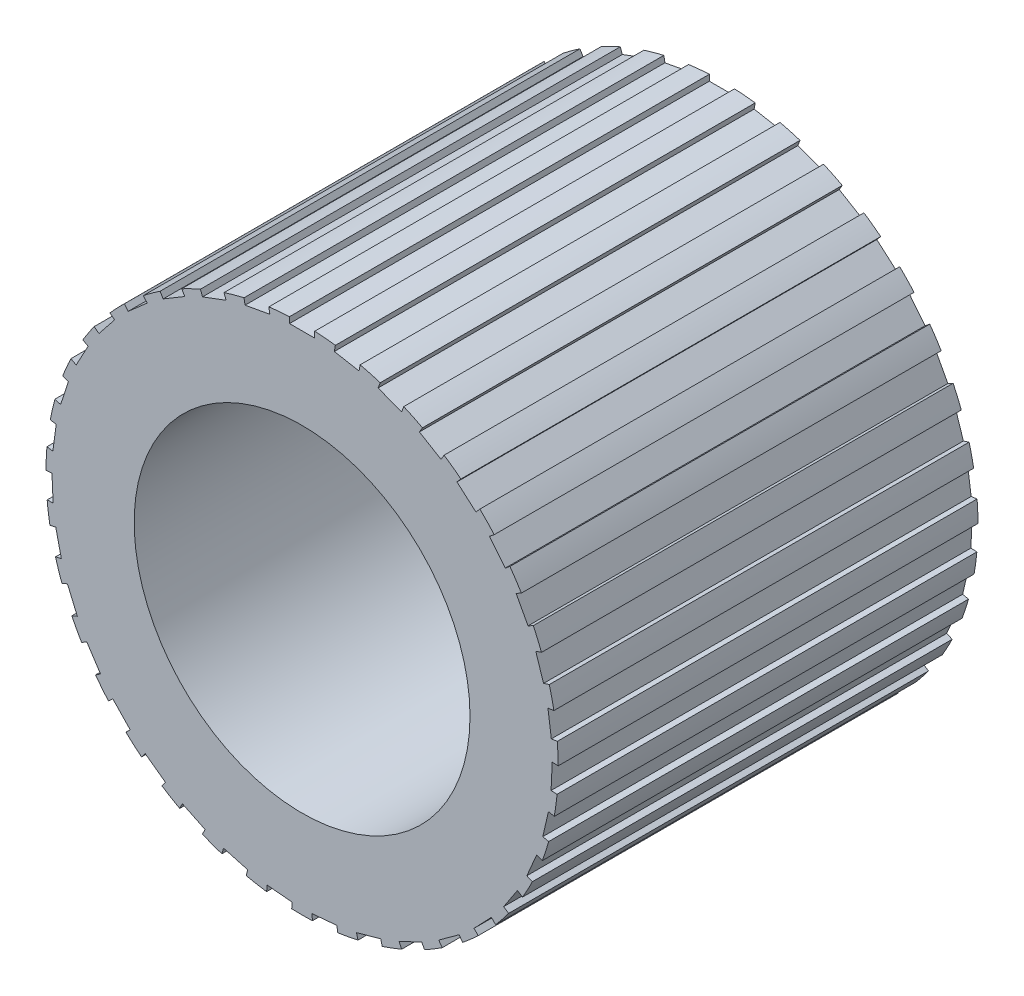
SolidWorks part; units mm, degrees
ref_plane "Plan de face" through (0, 0, 0) normal (0, 0, 1) x (1, 0, 0)
ref_plane "Plan de dessus" through (0, 0, 0) normal (0, 1, 0) x (1, 0, 0)
ref_plane "Plan de droite" through (0, 0, 0) normal (1, 0, 0) x (0, 0, -1)
sketch "Esquisse1" plane through (0, 0, 0) normal (0, 0, 1) x (1, 0, 0)
  circle A0 centre (0, 0) radius 6.1
  circle A1 centre (0, 0) radius 4
  dimension "D1" = 8
  dimension "D2" = 12.2
extrude "Boss.-Extru.1" add sketch "Esquisse1" along normal blind 10 contours A0 | A1
sketch "Esquisse4" plane through (0, 0, 10) normal (0, 0, 1) x (1, 0, 0)
  line L0 (0.7672, 5.9079) -> (0.8208, 6.2031)
  line L1 (-0.3, 5.95) -> (0.3, 5.95)
  line L2 (-0.3, 5.95) -> (-0.3, 6.25)
  line L3 (-0.3, 6.25) -> (0.3, 6.25)
  line L4 (0.3, 5.95) -> (0.3, 6.25)
  line L5 (-0.3, 5.95) -> (0.3, 6.25) construction
  line L6 (-0.3, 6.25) -> (0.3, 5.95) construction
  line L7 (0.7672, 5.9079) -> (1.3576, 5.8008)
  line L8 (1.3576, 5.8008) -> (1.4112, 6.096)
  line L9 (0.8208, 6.2031) -> (1.4112, 6.096)
  line L10 (1.8098, 5.676) -> (1.9152, 5.9569)
  line L11 (1.8098, 5.676) -> (2.3716, 5.4652)
  line L12 (2.3716, 5.4652) -> (2.477, 5.7461)
  line L13 (1.9152, 5.9569) -> (2.477, 5.7461)
  line L14 (2.7942, 5.2616) -> (2.9481, 5.5192)
  line L15 (2.7942, 5.2616) -> (3.3093, 4.9539)
  line L16 (3.3093, 4.9539) -> (3.4632, 5.2114)
  line L17 (2.9481, 5.5192) -> (3.4632, 5.2114)
  line L18 (3.6888, 4.6782) -> (3.8862, 4.9041)
  line L19 (3.6888, 4.6782) -> (4.1407, 4.2834)
  line L20 (4.1407, 4.2834) -> (4.338, 4.5093)
  line L21 (3.8862, 4.9041) -> (4.338, 4.5093)
  line L22 (4.4649, 3.9443) -> (4.6994, 4.1314)
  line L23 (4.4649, 3.9443) -> (4.8389, 3.4752)
  line L24 (4.8389, 3.4752) -> (5.0735, 3.6623)
  line L25 (4.6994, 4.1314) -> (5.0735, 3.6623)
  line L26 (5.0974, 3.0837) -> (5.3616, 3.2259)
  line L27 (5.0974, 3.0837) -> (5.3817, 2.5553)
  line L28 (5.3817, 2.5553) -> (5.6459, 2.6975)
  line L29 (5.3616, 3.2259) -> (5.6459, 2.6975)
  line L30 (5.5661, 2.124) -> (5.8514, 2.2167)
  line L31 (5.5661, 2.124) -> (5.7515, 1.5533)
  line L32 (5.7515, 1.5533) -> (6.0368, 1.646)
  line L33 (5.8514, 2.2167) -> (6.0368, 1.646)
  line L34 (5.8559, 1.096) -> (6.1532, 1.1362)
  line L35 (5.8559, 1.096) -> (5.9364, 0.5014)
  line L36 (5.9364, 0.5014) -> (6.2337, 0.5417)
  line L37 (6.1532, 1.1362) -> (6.2337, 0.5417)
  line L38 (5.9575, 0.0328) -> (6.2572, 0.0193)
  line L39 (5.9575, 0.0328) -> (5.9305, -0.5666)
  line L40 (5.9305, -0.5666) -> (6.2302, -0.5801)
  line L41 (6.2572, 0.0193) -> (6.2302, -0.5801)
  line L42 (5.8676, -1.0315) -> (6.1601, -1.0983)
  line L43 (5.8676, -1.0315) -> (5.7341, -1.6165)
  line L44 (5.7341, -1.6165) -> (6.0265, -1.6832)
  line L45 (6.1601, -1.0983) -> (6.0265, -1.6832)
  line L46 (5.5891, -2.0626) -> (5.865, -2.1805)
  line L47 (5.5891, -2.0626) -> (5.3533, -2.6144)
  line L48 (5.3533, -2.6144) -> (5.6291, -2.7323)
  line L49 (5.865, -2.1805) -> (5.6291, -2.7323)
  line L50 (5.131, -3.0275) -> (5.3814, -3.1927)
  line L51 (5.131, -3.0275) -> (4.8004, -3.5282)
  line L52 (4.8004, -3.5282) -> (5.0508, -3.6935)
  line L53 (5.3814, -3.1927) -> (5.0508, -3.6935)
  line L54 (4.5079, -3.895) -> (4.7248, -4.1023)
  line L55 (4.5079, -3.895) -> (4.0933, -4.3287)
  line L56 (4.0933, -4.3287) -> (4.3101, -4.536)
  line L57 (4.7248, -4.1023) -> (4.3101, -4.536)
  line L58 (3.74, -4.6373) -> (3.9164, -4.88)
  line L59 (3.74, -4.6373) -> (3.2546, -4.99)
  line L60 (3.2546, -4.99) -> (3.431, -5.2327)
  line L61 (3.9164, -4.88) -> (3.431, -5.2327)
  line L62 (2.8519, -5.2306) -> (2.9821, -5.5009)
  line L63 (2.8519, -5.2306) -> (2.3113, -5.4909)
  line L64 (2.3113, -5.4909) -> (2.4415, -5.7612)
  line L65 (2.9821, -5.5009) -> (2.4415, -5.7612)
  line L66 (1.8721, -5.6558) -> (1.9519, -5.945)
  line L67 (1.8721, -5.6558) -> (1.2937, -5.8154)
  line L68 (1.2937, -5.8154) -> (1.3735, -6.1046)
  line L69 (1.9519, -5.945) -> (1.3735, -6.1046)
  line L70 (0.8321, -5.8992) -> (0.859, -6.1979)
  line L71 (0.8321, -5.8992) -> (0.2346, -5.9529)
  line L72 (0.2346, -5.9529) -> (0.2615, -6.2517)
  line L73 (0.859, -6.1979) -> (0.2615, -6.2517)
  line L74 (-0.2346, -5.9529) -> (-0.2615, -6.2517)
  line L75 (-0.2346, -5.9529) -> (-0.8321, -5.8992)
  line L76 (-0.8321, -5.8992) -> (-0.859, -6.1979)
  line L77 (-0.2615, -6.2517) -> (-0.859, -6.1979)
  line L78 (-1.2937, -5.8154) -> (-1.3735, -6.1046)
  line L79 (-1.2937, -5.8154) -> (-1.8721, -5.6558)
  line L80 (-1.8721, -5.6558) -> (-1.9519, -5.945)
  line L81 (-1.3735, -6.1046) -> (-1.9519, -5.945)
  line L82 (-2.3113, -5.4909) -> (-2.4415, -5.7612)
  line L83 (-2.3113, -5.4909) -> (-2.8519, -5.2306)
  line L84 (-2.8519, -5.2306) -> (-2.9821, -5.5009)
  line L85 (-2.4415, -5.7612) -> (-2.9821, -5.5009)
  line L86 (-3.2546, -4.99) -> (-3.431, -5.2327)
  line L87 (-3.2546, -4.99) -> (-3.74, -4.6373)
  line L88 (-3.74, -4.6373) -> (-3.9164, -4.88)
  line L89 (-3.431, -5.2327) -> (-3.9164, -4.88)
  line L90 (-4.0933, -4.3287) -> (-4.3101, -4.536)
  line L91 (-4.0933, -4.3287) -> (-4.5079, -3.895)
  line L92 (-4.5079, -3.895) -> (-4.7248, -4.1023)
  line L93 (-4.3101, -4.536) -> (-4.7248, -4.1023)
  line L94 (-4.8004, -3.5282) -> (-5.0508, -3.6935)
  line L95 (-4.8004, -3.5282) -> (-5.131, -3.0275)
  line L96 (-5.131, -3.0275) -> (-5.3814, -3.1927)
  line L97 (-5.0508, -3.6935) -> (-5.3814, -3.1927)
  line L98 (-5.3533, -2.6144) -> (-5.6291, -2.7323)
  line L99 (-5.3533, -2.6144) -> (-5.5891, -2.0626)
  line L100 (-5.5891, -2.0626) -> (-5.865, -2.1805)
  line L101 (-5.6291, -2.7323) -> (-5.865, -2.1805)
  line L102 (-5.7341, -1.6165) -> (-6.0265, -1.6832)
  line L103 (-5.7341, -1.6165) -> (-5.8676, -1.0315)
  line L104 (-5.8676, -1.0315) -> (-6.1601, -1.0983)
  line L105 (-6.0265, -1.6832) -> (-6.1601, -1.0983)
  line L106 (-5.9305, -0.5666) -> (-6.2302, -0.5801)
  line L107 (-5.9305, -0.5666) -> (-5.9575, 0.0328)
  line L108 (-5.9575, 0.0328) -> (-6.2572, 0.0193)
  line L109 (-6.2302, -0.5801) -> (-6.2572, 0.0193)
  line L110 (-5.9364, 0.5014) -> (-6.2337, 0.5417)
  line L111 (-5.9364, 0.5014) -> (-5.8559, 1.096)
  line L112 (-5.8559, 1.096) -> (-6.1532, 1.1362)
  line L113 (-6.2337, 0.5417) -> (-6.1532, 1.1362)
  line L114 (-5.7515, 1.5533) -> (-6.0368, 1.646)
  line L115 (-5.7515, 1.5533) -> (-5.5661, 2.124)
  line L116 (-5.5661, 2.124) -> (-5.8514, 2.2167)
  line L117 (-6.0368, 1.646) -> (-5.8514, 2.2167)
  line L118 (-5.3817, 2.5553) -> (-5.6459, 2.6975)
  line L119 (-5.3817, 2.5553) -> (-5.0974, 3.0837)
  line L120 (-5.0974, 3.0837) -> (-5.3616, 3.2259)
  line L121 (-5.6459, 2.6975) -> (-5.3616, 3.2259)
  line L122 (-4.8389, 3.4752) -> (-5.0735, 3.6623)
  line L123 (-4.8389, 3.4752) -> (-4.4649, 3.9443)
  line L124 (-4.4649, 3.9443) -> (-4.6994, 4.1314)
  line L125 (-5.0735, 3.6623) -> (-4.6994, 4.1314)
  line L126 (-4.1407, 4.2834) -> (-4.338, 4.5093)
  line L127 (-4.1407, 4.2834) -> (-3.6888, 4.6782)
  line L128 (-3.6888, 4.6782) -> (-3.8862, 4.9041)
  line L129 (-4.338, 4.5093) -> (-3.8862, 4.9041)
  line L130 (-3.3093, 4.9539) -> (-3.4632, 5.2114)
  line L131 (-3.3093, 4.9539) -> (-2.7942, 5.2616)
  line L132 (-2.7942, 5.2616) -> (-2.9481, 5.5192)
  line L133 (-3.4632, 5.2114) -> (-2.9481, 5.5192)
  line L134 (-2.3716, 5.4652) -> (-2.477, 5.7461)
  line L135 (-2.3716, 5.4652) -> (-1.8098, 5.676)
  line L136 (-1.8098, 5.676) -> (-1.9152, 5.9569)
  line L137 (-2.477, 5.7461) -> (-1.9152, 5.9569)
  line L138 (-1.3576, 5.8008) -> (-1.4112, 6.096)
  line L139 (-1.3576, 5.8008) -> (-0.7672, 5.9079)
  line L140 (-0.7672, 5.9079) -> (-0.8208, 6.2031)
  line L141 (-1.4112, 6.096) -> (-0.8208, 6.2031)
  circle A0 centre (0, 0) radius 6.1 construction
  point P0 (0, 6.1)
  point P146 (0, 0)
  dimension "D1" = 0.3
  dimension "D2" = 0.6
  dimension "D3" = 35
extrude "Enlèv. mat.-Extru.3" cut sketch "Esquisse4" against normal blind 10
